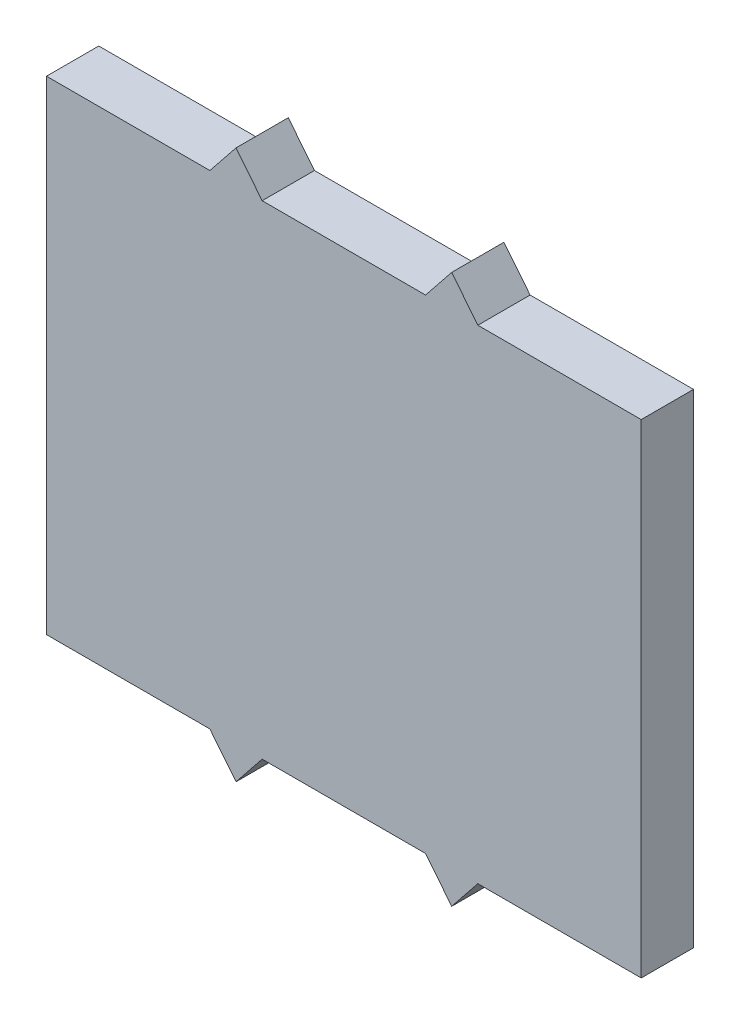
SolidWorks part; units mm, degrees
ref_plane "Front Plane" through (0, 0, 0) normal (0, 0, 1) x (1, 0, 0)
ref_plane "Top Plane" through (0, 0, 0) normal (0, 1, 0) x (1, 0, 0)
ref_plane "Right Plane" through (0, 0, 0) normal (1, 0, 0) x (0, 0, -1)
sketch "Sketch1" plane through (0, 0, 0) normal (0, 0, 1) x (1, 0, 0)
  line L0 (22.75, 37) -> (22.75, 14.7203) construction
  line L1 (0, 0) -> (45.5, 0)
  line L2 (0, 0) -> (0, 37)
  line L3 (0, 37) -> (45.5, 37)
  line L4 (45.5, 0) -> (45.5, 37)
  line L5 (12.5, 37) -> (14.5, 39.5)
  line L6 (14.5, 39.5) -> (16.5, 37)
  line L7 (31, 39.5) -> (29, 37)
  line L8 (33, 37) -> (31, 39.5)
  line L9 (0, 18.5) -> (57.9593, 18.5) construction
  line L10 (33, 0) -> (31, -2.5)
  line L11 (31, -2.5) -> (29, 0)
  line L12 (14.5, -2.5) -> (16.5, 0)
  line L13 (12.5, 0) -> (14.5, -2.5)
  point P9 (22.75, 37)
  point P16 (0, 18.5)
  point P17 (32, 38.25)
  point P18 (32, -1.25)
  dimension "D1" = 37
  dimension "D2" = 45.5
  dimension "D3" = 16.5
  dimension "D4" = 2.5
  dimension "D5" = 4
extrude "Basis" add sketch "Sketch1" along normal blind 4 contours L1 L4 L3 L2 | L6 L5 L3 | L3 L8 L7 | L1 L13 L12 | L11 L10 L1
sketch "Sketch3" [suppressed] plane through (0, 0, 4) normal (0, 0, 1) x (1, 0, 0)
  line L0 (22.75, 37) -> (22.75, 0) construction
  line L1 (16.5, 37) -> (29, 37) construction
  line L2 (16.5, 0) -> (29, 0) construction
  line L3 (0, 37) -> (12.5, 37) construction
  circle A0 centre (9.8, 25.6) radius 7.95
  circle A1 centre (35.7, 25.6) radius 7.95
  dimension "D3" = 15.9
  dimension "D1" = 11.4
  dimension "D2" = 25.9
extrude "HR04 gat " [suppressed] cut sketch "Sketch3" against normal up to surface (4 mm away)
sketch "Sketch4" [suppressed] plane through (0, 0, 4) normal (0, 0, 1) x (1, 0, 0)
  line L0 (7.7992, 12.9938) -> (37.7008, 12.9938) construction
  line L1 (16.5, 37) -> (29, 37) construction
  text T0 "AFSTAND SENSOR" font "Yu Gothic UI Semilight" height 3.5
  point P5 (22.75, 12.9938)
  point P8 (22.75, 37)
extrude "Afstand sensor" [suppressed] cut sketch "Sketch4" against normal blind 0.2
sketch "Sketch6" [suppressed] plane through (0, 0, 4) normal (0, 0, 1) x (1, 0, 0)
  line L4 (16.5, 37) -> (29, 37) construction
  point P0 (22.75, 31.8)
  point P3 (22.75, 37)
  line B0 (9.1, 31.8) -> (36.4, 31.8)
  line B1 (9.1, 31.8) -> (9.1, 16.3191)
  line B2 (9.1, 16.3191) -> (36.4, 16.3191)
  line B3 (36.4, 31.8) -> (36.4, 16.3191)
  circle B4 centre (11.1, 34.0981) radius 1.5
  circle B5 centre (34.4, 34.0981) radius 1.5
  circle B6 centre (34.4, 10.2981) radius 1.5
  circle B7 centre (11.1, 10.2981) radius 1.5
  dimension "D1" = 5.2
sketch_block_instance "Block1-1" [suppressed]
sketch_block "Block1" parameters "D1"=3, "D2"=3, "D3"=3, "D4"=3
extrude "Cut-Extrude5" [suppressed] cut sketch "Sketch6" against normal up to surface (4 mm away)
sketch "Sketch7" [suppressed] plane through (0, 0, 4) normal (0, 0, 1) x (1, 0, 0)
  line L0 (-2.0092, 11.0348) -> (47.5092, 11.0348) construction
  line L1 (16.5, 37) -> (29, 37) construction
  text T0 "oled scherm " font "Yu Gothic UI Semilight" height 3.5
  point P4 (22.75, 37)
  point P5 (22.75, 11.0348)
extrude "Cut-Extrude6" [suppressed] cut sketch "Sketch7" against normal blind 0.2
sketch "Sketch9" [suppressed] plane through (0, 0, 4) normal (0, 0, 1) x (1, 0, 0)
  line L0 (15.4564, 12.6867) -> (24.4394, 12.6867) construction
  text T0 "V0.2"
